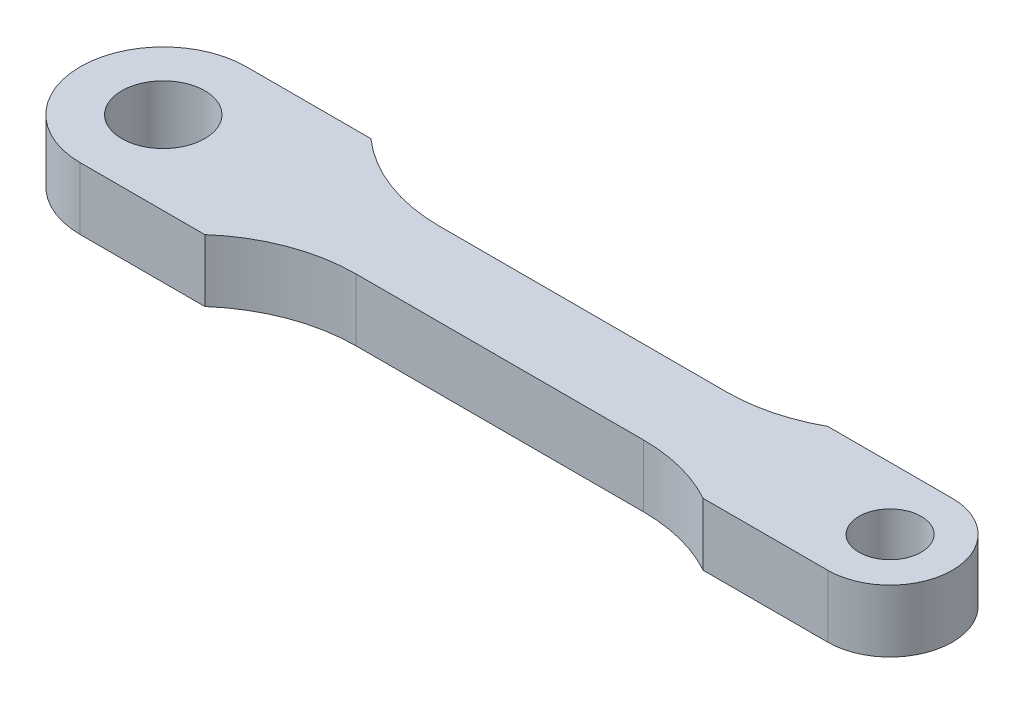
SolidWorks part; units mm, degrees
ref_plane "Front Plane" through (0, 0, 0) normal (0, 0, 1) x (1, 0, 0)
ref_plane "Top Plane" through (0, 0, 0) normal (0, 1, 0) x (1, 0, 0)
ref_plane "Right Plane" through (0, 0, 0) normal (1, 0, 0) x (0, 0, -1)
sketch "Эскиз1" plane through (0, 0, 0) normal (0, 1, 0) x (1, 0, 0)
  line L0 (0, 0) -> (35, 0) construction
  line L1 (0, -4) -> (6, -4)
  line L2 (11.2915, -2) -> (25.127, -2)
  line L3 (35, -3) -> (29, -3)
  line L4 (35, 3) -> (29, 3)
  line L5 (11.2915, 2) -> (25.127, 2)
  line L6 (0, 4) -> (6, 4)
  circle A0 centre (0, 0) radius 2
  arc A1 (0, 4) -> (0, -4) centre (0, 0) ccw
  circle A2 centre (35, 0) radius 1.5
  arc A3 (35, -3) -> (35, 3) centre (35, 0) ccw
  arc A5 (29, -3) -> (25.127, -2) centre (25.127, -10) ccw
  arc A6 (29, 3) -> (25.127, 2) centre (25.127, 10) cw
  arc A7 (11.2915, -2) -> (6, -4) centre (11.2915, -10) ccw
  arc A8 (11.2915, 2) -> (6, 4) centre (11.2915, 10) cw
  dimension "D1" = 4
  dimension "D2" = 8
  dimension "D3" = 3
  dimension "D4" = 6
  dimension "D9" = 6
  dimension "D5" = 35
  dimension "D6" = 6
  dimension "D7" = 4
extrude "Бобышка-Вытянуть1" add sketch "Эскиз1" along normal blind 3
